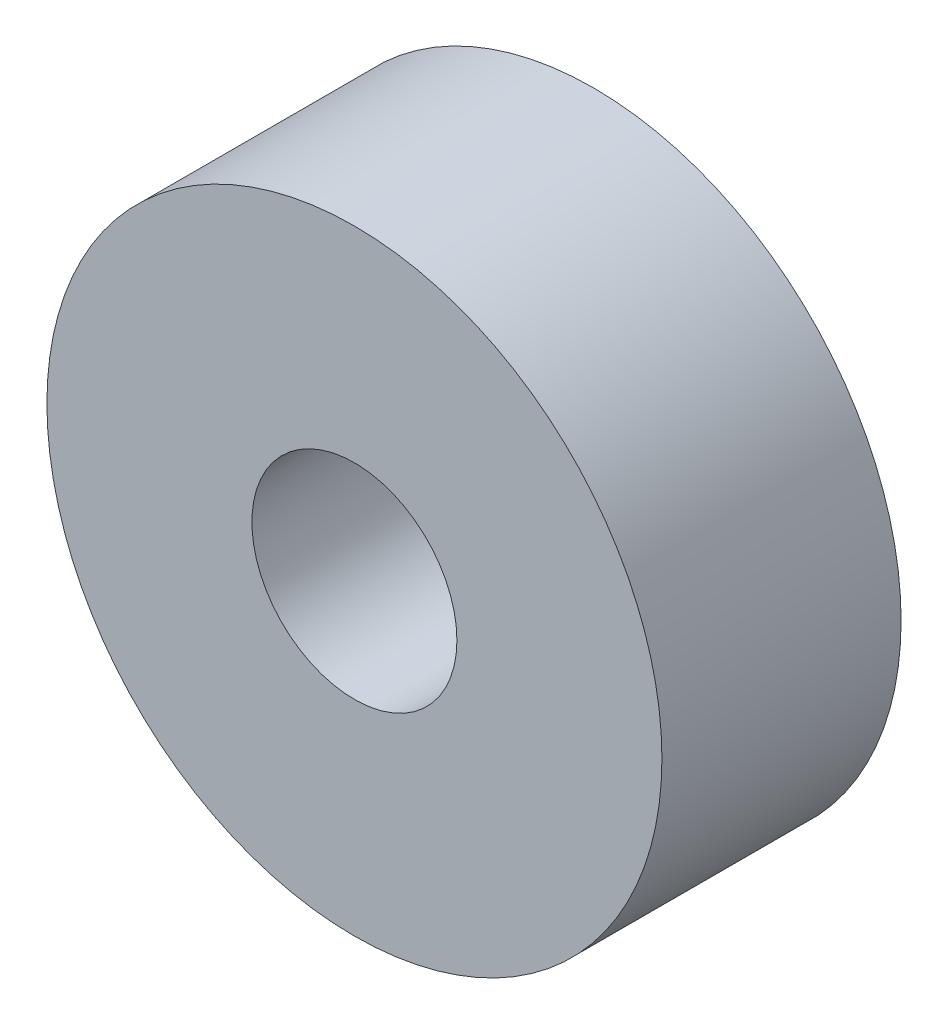
SolidWorks part; units mm, degrees
material "聚亚安酯(11671)"
ref_plane "前视基准面" through (0, 0, 0) normal (0, 0, 1) x (1, 0, 0)
ref_plane "上视基准面" through (0, 0, 0) normal (0, 1, 0) x (1, 0, 0)
ref_plane "右视基准面" through (0, 0, 0) normal (1, 0, 0) x (0, 0, -1)
sketch "草图1" plane through (0, 0, 0) normal (0, 0, 1) x (1, 0, 0)
  circle A0 centre (0, 0) radius 9
  circle A1 centre (0, 0) radius 3
  dimension "D1" = 18
  dimension "D2" = 6
extrude "凸台-拉伸1" add sketch "草图1" along normal blind 7
